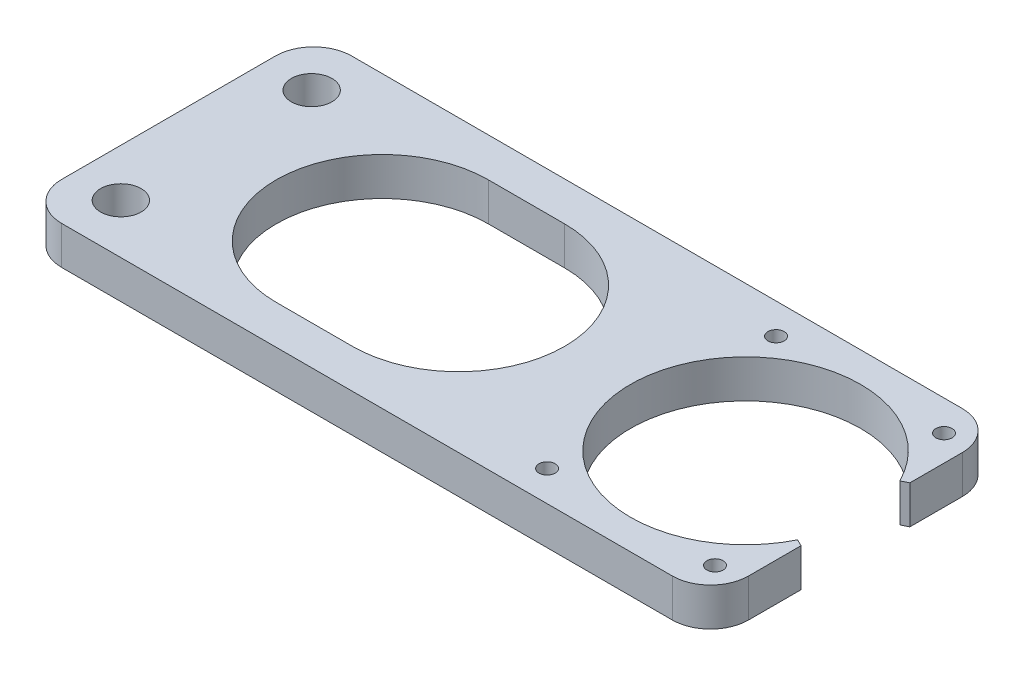
SolidWorks part; units mm, degrees
ref_plane "Front Plane" through (0, 0, 0) normal (0, 0, 1) x (1, 0, 0)
ref_plane "Top Plane" through (0, 0, 0) normal (0, 1, 0) x (1, 0, 0)
ref_plane "Right Plane" through (0, 0, 0) normal (1, 0, 0) x (0, 0, -1)
sketch "Sketch1" plane through (0, 0, 0) normal (0, 1, 0) x (1, 0, 0)
  line L0 (35.56, 24.13) -> (48.26, 24.13) construction
  line L1 (0, 0) -> (114.3, 0)
  line L2 (0, 0) -> (0, 48.26)
  line L3 (0, 48.26) -> (114.3, 48.26)
  line L4 (114.3, 0) -> (114.3, 15.0752)
  line L5 (35.56, 41.783) -> (48.26, 41.783)
  line L6 (35.56, 6.477) -> (48.26, 6.477)
  line L8 (113.1751, 32.6278) -> (114.3, 33.1848)
  line L9 (113.1751, 15.6322) -> (114.3, 15.0752)
  line L10 (114.3, 33.1848) -> (114.3, 48.26)
  arc A0 (35.56, 41.783) -> (35.56, 6.477) centre (35.56, 24.13) ccw
  arc A1 (48.26, 6.477) -> (48.26, 41.783) centre (48.26, 24.13) ccw
  arc A2 (113.1751, 32.6278) -> (113.1751, 15.6322) centre (96.012, 24.13) ccw
  point P7 (41.91, 24.13)
  point P19 (0, 0)
  dimension "D3" = 17.653
  dimension "D7" = 48.006
  dimension "D9" = 38.3032
  dimension "D1" = 48.26
  dimension "D2" = 114.3
  dimension "D4" = 24.13
  dimension "D5" = 35.56
  dimension "D6" = 12.7
  dimension "D8" = 96.012
  dimension "D10" = 24.13
  dimension "D11" = 15.0752
extrude "Boss-Extrude1" add sketch "Sketch1" along normal blind 6.35 contours L2 L3 L10 L8 A2 L9 L4 L1 | L6 A1 L5 A0
fillet "Fillet1" radius 6.35 4 edges at (0, 3.175, -48.26) (114.3, 3.175, 0) (0, 3.175, 0) (114.3, 3.175, -48.26)
hole_wizard "1/4 Clearance Hole1" positions "Sketch2" profile "Sketch3" hole size "1/4" standard "ANSI Inch" end condition through all
sketch "Sketch2" plane through (0, 6.35, 0) normal (0, 1, 0) x (1, 0, 0)
  line L0 (6.35, 48.26) -> (107.95, 48.26) construction
  line L2 (0, 6.35) -> (0, 41.91) construction
  point P0 (7.9375, 40.005)
  point P2 (7.9375, 8.255)
  dimension "D1" = 31.75
  dimension "D2" = 8.255
  dimension "D3" = 7.9375
sketch "Sketch3" plane through (7.9375, 6.35, -40.005) normal (1, 0, 0) x (0, 0, 1)
  line L0 (0, 0) -> (0, 6.35)
  line L1 (0, 6.35) -> (3.3782, 6.35)
  line L2 (3.3782, 6.35) -> (3.3782, 0)
  line L5 (3.3782, 0) -> (0, 0)
  line L11 (0, -6.35) -> (0, 107.95) construction
  dimension "Thru Hole Dia." = 6.7564
  dimension "Thru Hole Depth" = 6.35
hole_wizard "Tap Drill for #6-32 Tap1" positions "Sketch4" profile "Sketch5" hole size "#6-32" standard "ANSI Inch" end condition through all
sketch "Sketch4" plane through (0, 6.35, 0) normal (0, 1, 0) x (1, 0, 0)
  line L1 (109.982, 5.08) -> (82.042, 5.08) construction
  line L2 (109.982, 5.08) -> (109.982, 43.18) construction
  line L3 (109.982, 43.18) -> (82.042, 43.18) construction
  line L4 (82.042, 5.08) -> (82.042, 43.18) construction
  line L5 (109.982, 5.08) -> (82.042, 43.18) construction
  line L6 (109.982, 43.18) -> (82.042, 5.08) construction
  point P0 (82.042, 43.18)
  point P2 (109.982, 43.18)
  point P4 (109.982, 5.08)
  point P6 (82.042, 5.08)
  point P9 (96.012, 24.13)
  point P347 (109.982, 43.18)
  point P348 (0, 0)
  point P349 (109.982, 5.08)
  point P350 (82.042, 5.08)
  point P351 (82.042, 43.18)
  point P352 (0, 0)
  point P353 (0, 0)
  dimension "D1" = 38.1
  dimension "D2" = 27.94
sketch "Sketch5" plane through (82.042, 6.35, -43.18) normal (1, 0, 0) x (0, 0, 1)
  line L0 (0, 0) -> (0, 6.35)
  line L1 (0, 6.35) -> (1.3525, 6.35)
  line L2 (1.3525, 6.35) -> (1.3525, 0)
  line L5 (1.3525, 0) -> (0, 0)
  line L11 (0, -6.35) -> (0, 107.95) construction
  dimension "Thru Hole Dia." = 2.7051
  dimension "Thru Hole Depth" = 6.35
